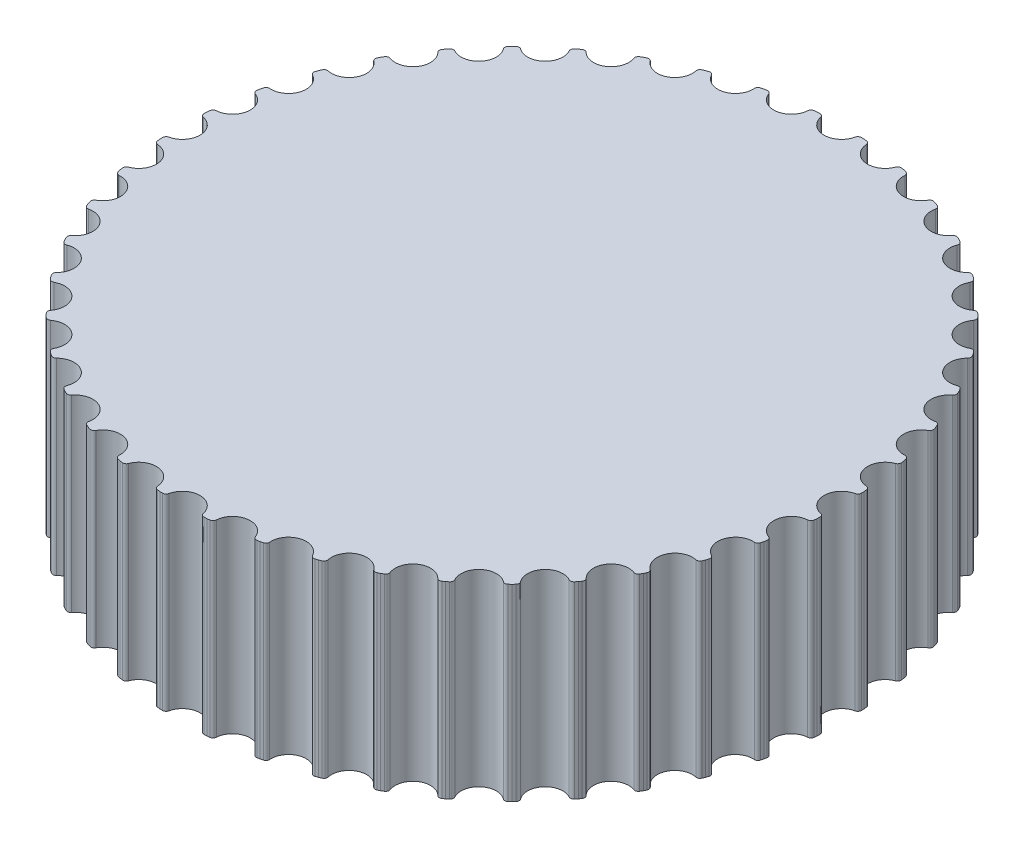
SolidWorks part; units mm, degrees
ref_plane "Front Plane" through (0, 0, 0) normal (0, 0, 1) x (1, 0, 0)
ref_plane "Top Plane" through (0, 0, 0) normal (0, 1, 0) x (1, 0, 0)
ref_plane "Right Plane" through (0, 0, 0) normal (1, 0, 0) x (0, 0, -1)
sketch "Sketch1" plane through (0, 0, 0) normal (0, 1, 0) x (1, 0, 0)
  circle A0 centre (0, 0) radius 14.015
  dimension "D1" = 28.03
extrude "Boss-Extrude1" add sketch "Sketch1" along normal blind 8
sketch "Sketch2" plane through (0, 8, 0) normal (0, 1, 0) x (1, 0, 0)
  line L0 (0, 0) -> (0, 14.01) construction
  line L1 (-0.8793, 13.968) -> (-1, 13.968)
  line L2 (0.8793, 13.968) -> (1, 13.968)
  line L3 (-1, 13.968) -> (-1, 14.1645)
  line L4 (-1, 14.1645) -> (1, 14.1645)
  line L5 (1, 14.1645) -> (1, 13.968)
  arc A0 (-0.7327, 13.85) -> (0.7327, 13.85) centre (0, 14.01) ccw
  arc A1 (-0.7327, 13.85) -> (-0.8793, 13.968) centre (-0.8793, 13.818) ccw
  arc A2 (0.7327, 13.85) -> (0.8793, 13.968) centre (0.8793, 13.818) cw
  dimension "D1" = 0.75
  dimension "D2" = 0.16
  dimension "D4" = 14.01
  dimension "D6" = 0
  dimension "D7" = 1
  dimension "D5" = 0.15
extrude "Cut-Extrude1" cut sketch "Sketch2" against normal through all
pattern_circular "CirPattern1" count 44 over 360 about axis through (0, 0, 0) along (0, 1, 0) of "Cut-Extrude1"
